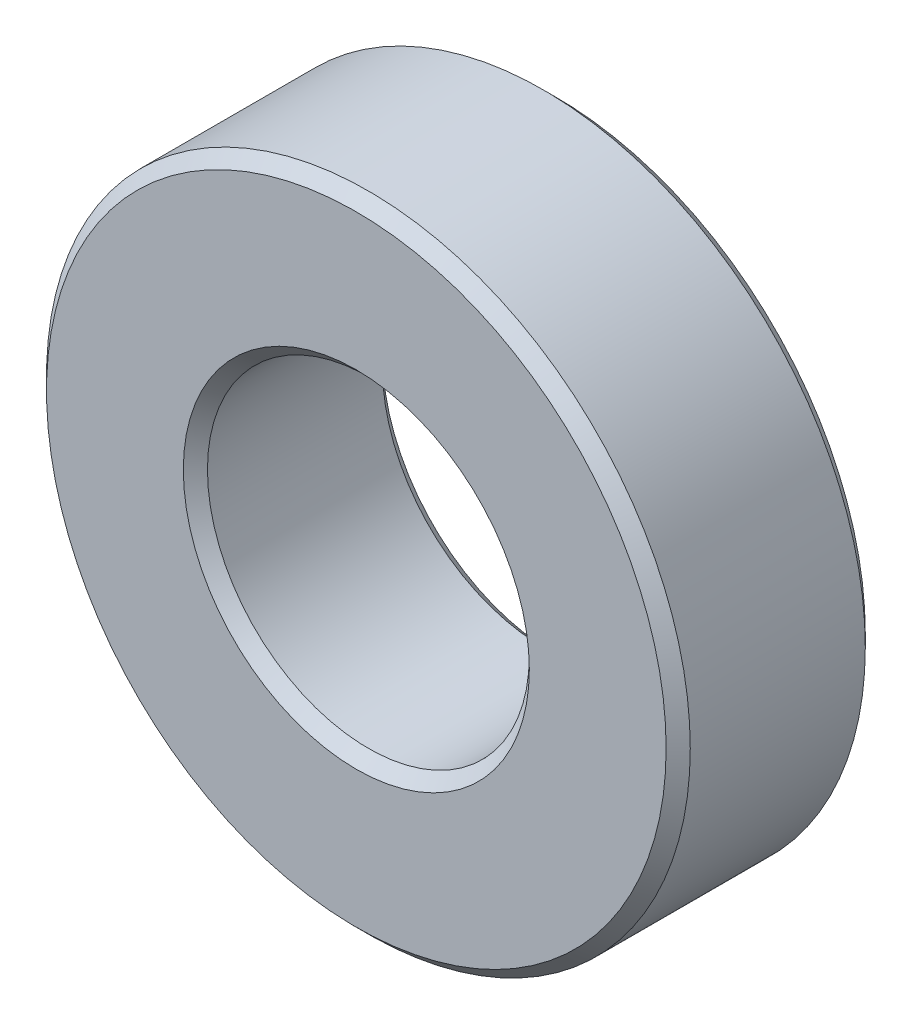
SolidWorks part; units mm, degrees
ref_plane "Front Plane" through (0, 0, 0) normal (0, 0, 1) x (1, 0, 0)
ref_plane "Top Plane" through (0, 0, 0) normal (0, 1, 0) x (1, 0, 0)
ref_plane "Right Plane" through (0, 0, 0) normal (1, 0, 0) x (0, 0, -1)
sketch "Sketch1" plane through (0, 0, 0) normal (0, 0, 1) x (1, 0, 0)
  circle A0 centre (0, 0) radius 4
  circle A1 centre (0, 0) radius 8
  dimension "D1" = 16
  dimension "D2" = 8
extrude "Boss-Extrude1" add sketch "Sketch1" along normal blind 4.95
chamfer "Chamfer1" distance 0.3 angle 45 4 edges at (4, 0, 0) (8, 0, 0) (4, 0, 4.95) (8, 0, 4.95)
